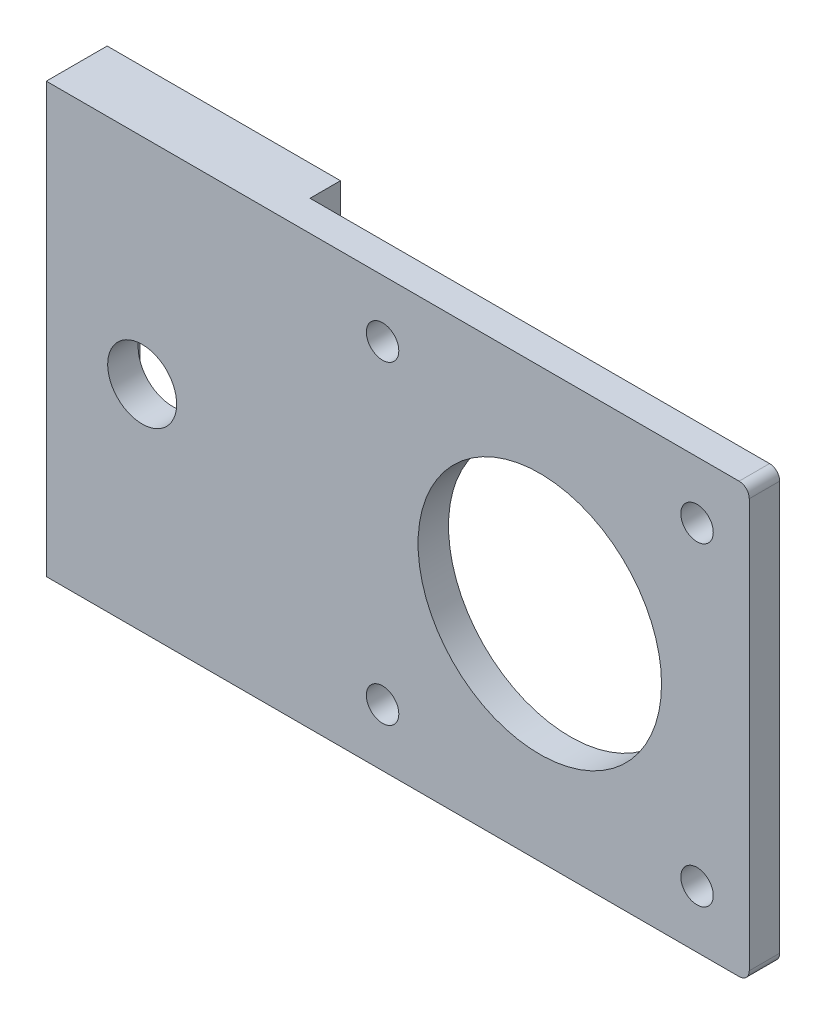
SolidWorks part; units mm, degrees
ref_plane "正面" through (0, 0, 0) normal (0, 0, 1) x (1, 0, 0)
ref_plane "平面" through (0, 0, 0) normal (0, 1, 0) x (1, 0, 0)
ref_plane "右側面" through (0, 0, 0) normal (1, 0, 0) x (0, 0, -1)
sketch "Sketch3" plane through (0, 0, 0) normal (0, 0, 1) x (1, 0, 0)
  line L1 (0, 0) -> (42.3, 0)
  line L2 (0, 0) -> (0, 42.3)
  line L3 (0, 42.3) -> (42.3, 42.3)
  line L4 (42.3, 0) -> (42.3, 42.3)
  line L5 (0, 42.3) -> (-4, 42.3)
  line L6 (0, 42.3) -> (0, 0)
  line L7 (0, 0) -> (-4, 0)
  line L8 (-4, 42.3) -> (-4, 0)
  dimension "D1" = 42.3
  dimension "D2" = 42.3
  dimension "D3" = 4
extrude "Boss-Extrude4" add sketch "Sketch3" along normal blind 3 contours L1 L4 L3 L5 L8 L7
sketch "Sketch10" plane through (-4, 0, 0) normal (-1, 0, 0) x (0, 0, 1)
  line L1 (3, 42.3) -> (-3, 42.3)
  line L2 (3, 42.3) -> (3, 0)
  line L3 (3, 0) -> (-3, 0)
  line L4 (-3, 42.3) -> (-3, 0)
  dimension "D1" = 6
extrude "Boss-Extrude5" add sketch "Sketch10" along normal blind 3
sketch "Sketch11" plane through (0, 0, 3) normal (0, 0, 1) x (1, 0, 0)
  line L0 (42.3, 42.3) -> (-7, 42.3) construction
  line L4 (17.65, 42.3) -> (17.65, 0)
  line L5 (42.3, 0) -> (-7, 0) construction
  line L6 (21.65, 42.3) -> (21.65, 0)
  line L7 (-7, 0) -> (-7, 42.3) construction
  line L8 (-7, 21.15) -> (42.3, 21.15)
  line L9 (42.3, 0) -> (42.3, 42.3) construction
  circle A0 centre (21.65, 21.15) radius 12
  circle A1 centre (6.15, 36.65) radius 1.6
  circle A2 centre (37.15, 36.65) radius 1.6
  circle A3 centre (37.15, 5.65) radius 1.6
  circle A4 centre (6.15, 5.65) radius 1.6
  dimension "D2" = 3.2
  dimension "D3" = 3.2
  dimension "D4" = 3.2
  dimension "D5" = 3.2
  dimension "D6" = 31
  dimension "D7" = 31
  dimension "D9" = 15.5
  dimension "D10" = 15.5
  dimension "D11" = 15.5
  dimension "D12" = 15.5
  dimension "D1" = 4
  dimension "D8" = 15.5
extrude "Cut-Extrude1" cut sketch "Sketch11" against normal through all contours A1 | A0 | A4 | A3 | A2
sketch "Sketch15" plane through (-7, 0, 0) normal (-1, 0, 0) x (0, 0, 1)
  line L0 (3, 42.3) -> (-3, 42.3) construction
  line L1 (3, 42.3) -> (0, 42.3)
  line L2 (3, 42.3) -> (3, 0)
  line L3 (3, 0) -> (0, 0)
  line L4 (0, 42.3) -> (0, 0)
  line L5 (-3, 0) -> (3, 0) construction
  line L6 (3, 0) -> (3, 42.3) construction
  dimension "D1" = 3
extrude "Boss-Extrude8" add sketch "Sketch15" along normal blind 20
sketch "Sketch16" plane through (0, 0, 0) normal (0, 0, -1) x (-1, 0, 0)
  line L0 (17.55, 42.3) -> (17.55, 0)
  line L1 (27, 42.3) -> (7, 42.3) construction
  line L2 (27, 0) -> (7, 0) construction
  line L4 (27, 42.3) -> (27, 0) construction
  line L5 (27, 21.15) -> (17.55, 21.15)
  circle A0 centre (17.55, 21.15) radius 3.4
  dimension "D2" = 9.45
  dimension "D1" = 6.8
fillet "Fillet5" radius 1 2 edges at (42.3, 42.3, 1.5) (42.3, 0, 1.5)
extrude "Cut-Extrude5" cut sketch "Sketch16" against normal through all contours A0
sketch "Sketch23" plane through (0, 0, 0) normal (0, 0, -1) x (-1, 0, 0)
  line L0 (27, 42.3) -> (27, 0) construction
  line L1 (7, 0) -> (27, 0)
  line L2 (7, 0) -> (7, 42.3)
  line L3 (7, 42.3) -> (27, 42.3)
  line L4 (27, 0) -> (27, 42.3)
extrude "Boss-Extrude9" add sketch "Sketch23" along normal blind 3
sketch "Sketch26" plane through (0, 0, -3) normal (0, 0, -1) x (-1, 0, 0)
  line L0 (17.55, 42.3) -> (17.55, 0)
  line L3 (27, 21.15) -> (4, 21.15)
  line L4 (27, 0) -> (27, 42.3) construction
  line L5 (4, 42.3) -> (4, 0) construction
  line L6 (27, 42.3) -> (4, 42.3) construction
  line L7 (27, 0) -> (4, 0) construction
  line L9 (23.75, 14.5) -> (11.35, 14.5)
  line L10 (23.75, 14.5) -> (23.75, 27.8)
  line L11 (23.75, 27.8) -> (11.35, 27.8)
  line L12 (11.35, 14.5) -> (11.35, 27.8)
  line L13 (23.75, 14.5) -> (11.35, 27.8) construction
  line L14 (23.75, 27.8) -> (11.35, 14.5) construction
  point P12 (17.55, 21.15)
  dimension "D1" = 9.45
  dimension "D2" = 13.3
  dimension "D3" = 12.4
extrude "Cut-Extrude7" cut sketch "Sketch26" against normal blind 3 contours L11 L12 L9 L10
